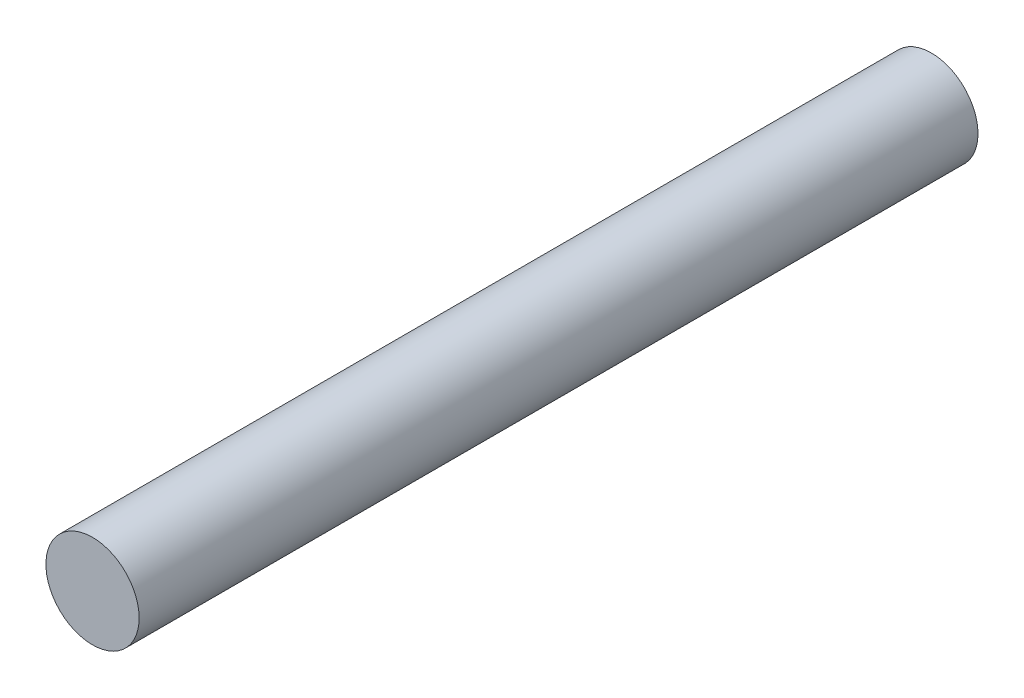
SolidWorks part; units mm, degrees
ref_plane "Front Plane" through (0, 0, 0) normal (0, 0, 1) x (1, 0, 0)
ref_plane "Top Plane" through (0, 0, 0) normal (0, 1, 0) x (1, 0, 0)
ref_plane "Right Plane" through (0, 0, 0) normal (1, 0, 0) x (0, 0, -1)
sketch "Sketch1" plane through (0, 0, 0) normal (0, 0, 1) x (1, 0, 0)
  circle A0 centre (0, 0) radius 4
  dimension "D1" = 8
extrude "Boss-Extrude1" add sketch "Sketch1" along normal blind 72
